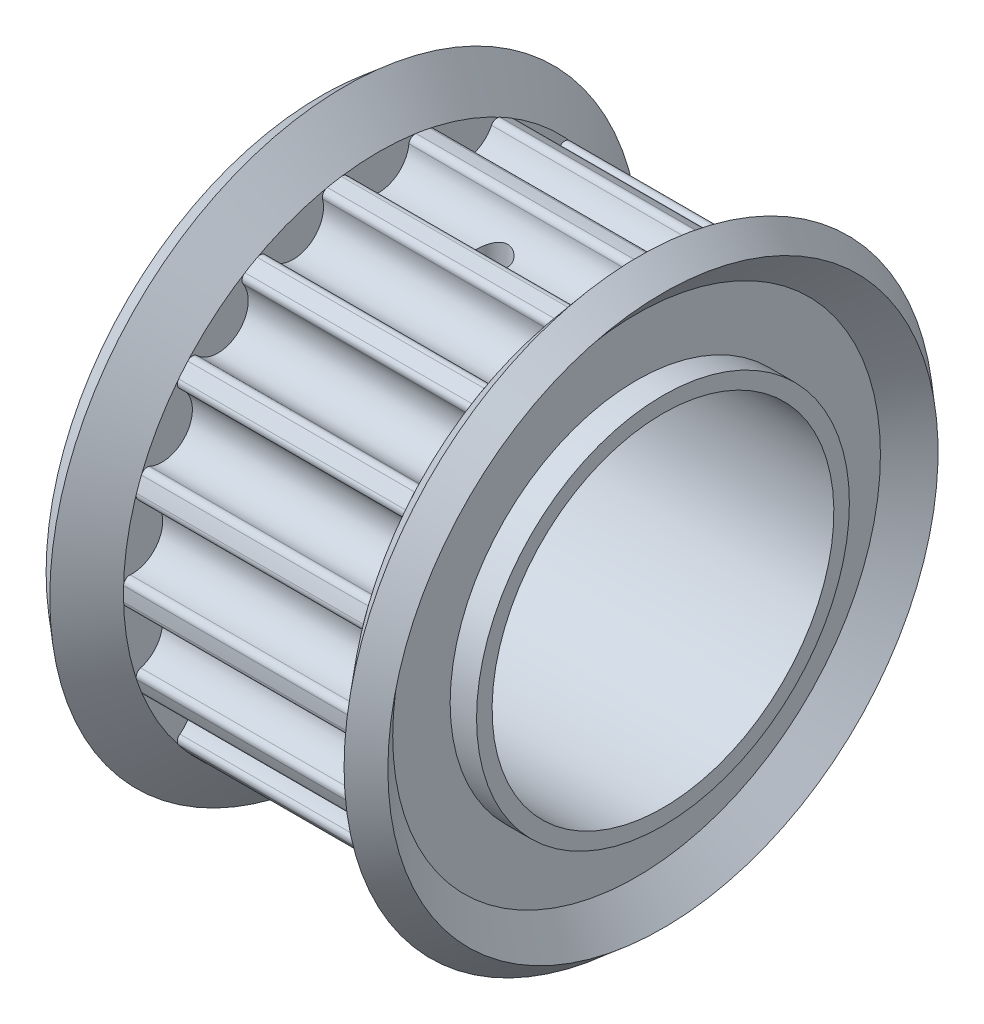
SolidWorks part; units mm, degrees
material "2014-T6"
ref_plane "Front Plane" through (0, 0, 0) normal (0, 0, 1) x (1, 0, 0)
ref_plane "Top Plane" through (0, 0, 0) normal (0, 1, 0) x (1, 0, 0)
ref_plane "Right Plane" through (0, 0, 0) normal (1, 0, 0) x (0, 0, -1)
sketch "Sketch1" plane through (0, 0, 0) normal (0, 0, 1) x (1, 0, 0)
  line L0 (-5.5, 4) -> (5.5, 4)
  line L1 (5.5, 4) -> (5.5, 6)
  line L2 (5.5, 6) -> (3.65, 6)
  line L3 (3.65, 6) -> (3.65, 8.215)
  line L4 (3.65, 8.215) -> (-3.65, 8.215)
  line L5 (-3.65, 8.215) -> (-3.65, 6)
  line L6 (-3.65, 6) -> (-5.5, 6)
  line L7 (-5.5, 6) -> (-5.5, 4)
  line L8 (0, 0) -> (0, 68.2564) construction
  line L9 (-16.0415, 0) -> (16.0415, 0) construction
  line L10 (-3.65, 8.595) -> (3.65, 8.595) construction
  dimension "D1" = 16.43
  dimension "D2" = 8
  dimension "D3" = 11
  dimension "D4" = 7.3
  dimension "D5" = 17.19
  dimension "D6" = 12
revolve "Revolve1" add sketch "Sketch1" angle 360 about L9
sketch "Sketch2" plane through (0, 0, 0) normal (1, 0, 0) x (0, 0, -1)
  line L0 (0, 7.075) -> (0, 8.215) construction
  line L1 (0, 8.215) -> (0, 8.595) construction
  line L3 (0, 0) -> (0, 68.2564) construction
  line L4 (1.2, 8.1269) -> (-1.2, 8.1269) construction
  circle A0 centre (0, 0) radius 8.595 construction
  arc A1 (1.2, 8.1269) -> (-1.2, 8.1269) centre (0, 0) ccw
  circle A2 centre (0, 0) radius 8.215 construction
  circle A3 centre (0, 0) radius 7.075 construction
  arc A4 (-0.9719, 7.95) -> (0.9719, 7.95) centre (0, 8.0523) ccw
  arc A5 (-1.2, 8.1269) -> (-0.9719, 7.95) centre (-1.1708, 7.929) cw
  arc A6 (1.2, 8.1269) -> (0.9719, 7.95) centre (1.1708, 7.929) ccw
  dimension "D2" = 0.2
  dimension "D1" = 1.14
  dimension "D3" = 2.4
extrude "Cut-Extrude1" cut sketch "Sketch2" against normal through all and the other way through all
pattern_circular "CirPattern1" count 18 over 360 about axis through (0, 0, 0) along (1, 0, 0) of "Cut-Extrude1"
sketch "Sketch3" plane through (0, 0, 0) normal (0, 0, 1) x (1, 0, 0)
  line L0 (3.65, 6) -> (4.65, 6)
  line L1 (3.65, 6) -> (3.65, 8.215)
  line L2 (3.65, 8.215) -> (4.7363, 9.5)
  line L3 (4.7363, 9.5) -> (5.5, 8.8544)
  line L4 (5.5, 8.8544) -> (4.65, 7.8489)
  line L5 (4.65, 7.8489) -> (4.65, 6)
  line L6 (0, 0) -> (16.0415, 0) construction
  line L7 (0, 0) -> (0, 11.7154) construction
  line L8 (0, 0) -> (0, 68.2564) construction
  line L9 (-3.65, 6) -> (-3.65, 8.215)
  line L10 (-3.65, 6) -> (-4.65, 6)
  line L11 (-4.65, 7.8489) -> (-4.65, 6)
  line L12 (-5.5, 8.8544) -> (-4.65, 7.8489)
  line L13 (-4.7363, 9.5) -> (-5.5, 8.8544)
  line L14 (-3.65, 8.215) -> (-4.7363, 9.5)
  dimension "D1" = 1.85
  dimension "D2" = 19
  dimension "D3" = 1
revolve "Revolve2" add sketch "Sketch3" angle 360 about L6
sketch "Sketch4" plane through (0, 0, 0) normal (0, 0, 1) x (1, 0, 0)
  line L0 (0, 0) -> (-15.4218, 0) construction
  line L1 (-5.5, 5.5) -> (5.5, 5.5)
  line L2 (-5.5, 5.5) -> (-5.5, 0)
  line L3 (-5.5, 0) -> (5.5, 0)
  line L4 (5.5, 5.5) -> (5.5, 0)
  line L5 (5.5, -4) -> (5.5, 4) construction
  line L6 (-5.5, 4) -> (-5.5, -4) construction
  dimension "D1" = 11
revolve "Cut-Revolve1" cut sketch "Sketch4" angle 360 about L0
sketch "Sketch5" plane through (0, 0, 0) normal (0, 1, 0) x (1, 0, 0)
  circle A0 centre (0, 0) radius 0.5
  dimension "D1" = 1
extrude "Cut-Extrude2" cut sketch "Sketch5" along normal through all
